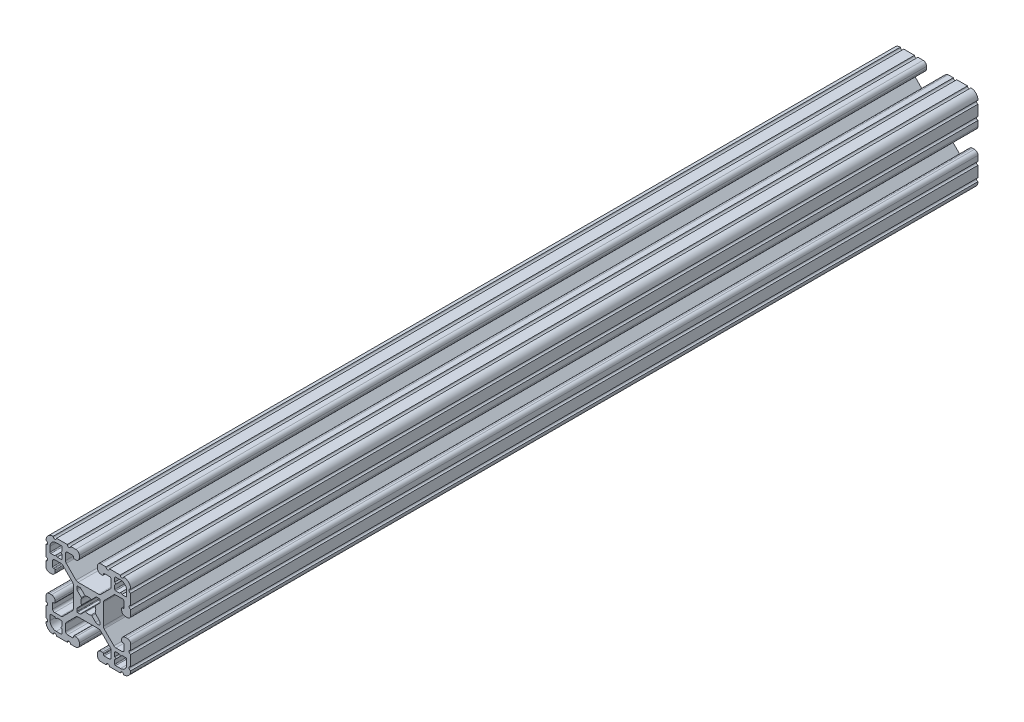
SolidWorks part; units mm, degrees
ref_plane "Front Plane" through (0, 0, 0) normal (0, 0, 1) x (1, 0, 0)
ref_plane "Top Plane" through (0, 0, 0) normal (0, 1, 0) x (1, 0, 0)
ref_plane "Right Plane" through (0, 0, 0) normal (1, 0, 0) x (0, 0, -1)
ref_plane "Plane1" through (0, 0, -2322.576) normal (0, 0, -1) x (-1, 0, 0)
sketch "Sketch1" plane through (0, 0, -2322.576) normal (0, 0, -1) x (-1, 0, 0)
  line L0 (17.2466, 14.4526) -> (17.2466, 12.2428)
  line L1 (16.8656, 11.8618) -> (15.0927, 11.8618)
  line L2 (15.0927, 11.8618) -> (14.5542, 12.4003)
  line L3 (14.5542, 12.4003) -> (14.0157, 11.8618)
  line L4 (14.0157, 11.8618) -> (12.2428, 11.8618)
  line L5 (11.8618, 12.2428) -> (11.8618, 14.0157)
  line L6 (11.8618, 14.0157) -> (12.4003, 14.5542)
  line L7 (12.4003, 14.5542) -> (11.8618, 15.0927)
  line L8 (11.8618, 15.0927) -> (11.8618, 16.8656)
  line L9 (12.2428, 17.2466) -> (14.4526, 17.2466)
  line L10 (17.2466, -12.2428) -> (17.2466, -14.4526)
  line L11 (14.4526, -17.2466) -> (12.2428, -17.2466)
  line L12 (11.8618, -16.8656) -> (11.8618, -15.0927)
  line L13 (11.8618, -15.0927) -> (12.4003, -14.5542)
  line L14 (12.4003, -14.5542) -> (11.8618, -14.0157)
  line L15 (11.8618, -14.0157) -> (11.8618, -12.2428)
  line L16 (12.2428, -11.8618) -> (14.0157, -11.8618)
  line L17 (14.0157, -11.8618) -> (14.5542, -12.4003)
  line L18 (14.5542, -12.4003) -> (15.0927, -11.8618)
  line L19 (15.0927, -11.8618) -> (16.8656, -11.8618)
  line L20 (5.1689, -3.9207) -> (5.1689, -4.9149)
  line L21 (4.9149, -5.1689) -> (3.9207, -5.1689)
  line L22 (3.2921, -4.9085) -> (1.5823, -3.1988)
  line L23 (-1.5823, -3.1988) -> (-3.2921, -4.9085)
  line L24 (-3.9207, -5.1689) -> (-4.9149, -5.1689)
  line L25 (-5.1689, -4.9149) -> (-5.1689, -3.9207)
  line L26 (-4.9085, -3.2921) -> (-3.1988, -1.5823)
  line L27 (-3.1988, 1.5823) -> (-4.9085, 3.2921)
  line L28 (-5.1689, 3.9207) -> (-5.1689, 4.9149)
  line L29 (-4.9149, 5.1689) -> (-3.9207, 5.1689)
  line L30 (-3.2921, 4.9085) -> (-1.5823, 3.1988)
  line L31 (1.5823, 3.1988) -> (3.2921, 4.9085)
  line L32 (3.9207, 5.1689) -> (4.9149, 5.1689)
  line L33 (5.1689, 4.9149) -> (5.1689, 3.9207)
  line L34 (4.9085, 3.2921) -> (3.1988, 1.5823)
  line L35 (3.1988, -1.5823) -> (4.9085, -3.2921)
  line L36 (-11.8618, -12.2428) -> (-11.8618, -14.0157)
  line L37 (-11.8618, -14.0157) -> (-12.4003, -14.5542)
  line L38 (-12.4003, -14.5542) -> (-11.8618, -15.0927)
  line L39 (-11.8618, -15.0927) -> (-11.8618, -16.8656)
  line L40 (-12.2428, -17.2466) -> (-14.4526, -17.2466)
  line L41 (-17.2466, -14.4526) -> (-17.2466, -12.2428)
  line L42 (-16.8656, -11.8618) -> (-15.0927, -11.8618)
  line L43 (-15.0927, -11.8618) -> (-14.5542, -12.4003)
  line L44 (-14.5542, -12.4003) -> (-14.0157, -11.8618)
  line L45 (-14.0157, -11.8618) -> (-12.2428, -11.8618)
  line L46 (-11.8618, 16.8656) -> (-11.8618, 15.0927)
  line L47 (-11.8618, 15.0927) -> (-12.4003, 14.5542)
  line L48 (-12.4003, 14.5542) -> (-11.8618, 14.0157)
  line L49 (-11.8618, 14.0157) -> (-11.8618, 12.2428)
  line L50 (-12.2428, 11.8618) -> (-14.0157, 11.8618)
  line L51 (-14.0157, 11.8618) -> (-14.5542, 12.4003)
  line L52 (-14.5542, 12.4003) -> (-15.0927, 11.8618)
  line L53 (-15.0927, 11.8618) -> (-16.8656, 11.8618)
  line L54 (-17.2466, 12.2428) -> (-17.2466, 14.4526)
  line L55 (-14.4526, 17.2466) -> (-12.2428, 17.2466)
  line L56 (19.05, -14.3256) -> (19.05, -9.4996)
  line L57 (19.05, -7.9756) -> (19.05, -5.6388)
  line L58 (17.4752, -4.064) -> (16.5608, -4.064)
  line L59 (14.986, -5.6388) -> (14.986, -6.35)
  line L60 (15.367, -6.731) -> (15.6972, -6.731)
  line L61 (16.0782, -7.112) -> (16.0782, -9.398)
  line L62 (15.1892, -10.287) -> (12.3756, -10.287)
  line L63 (11.4776, -9.915) -> (7.1157, -5.5531)
  line L64 (6.7437, -4.6551) -> (6.7437, 4.6551)
  line L65 (7.1157, 5.5531) -> (11.4776, 9.915)
  line L66 (12.3756, 10.287) -> (15.1892, 10.287)
  line L67 (16.0782, 9.398) -> (16.0782, 7.112)
  line L68 (15.6972, 6.731) -> (15.367, 6.731)
  line L69 (14.986, 6.35) -> (14.986, 5.6388)
  line L70 (16.5608, 4.064) -> (17.4752, 4.064)
  line L71 (19.05, 5.6388) -> (19.05, 7.9756)
  line L72 (19.05, 9.4996) -> (19.05, 14.3256)
  line L73 (14.3256, 19.05) -> (9.4996, 19.05)
  line L74 (7.9756, 19.05) -> (5.6388, 19.05)
  line L75 (4.064, 17.4752) -> (4.064, 16.5608)
  line L76 (5.6388, 14.986) -> (6.35, 14.986)
  line L77 (6.731, 15.367) -> (6.731, 15.6972)
  line L78 (7.112, 16.0782) -> (9.398, 16.0782)
  line L79 (10.287, 15.1892) -> (10.287, 12.3756)
  line L80 (9.915, 11.4776) -> (5.5531, 7.1157)
  line L81 (4.6551, 6.7437) -> (-4.6551, 6.7437)
  line L82 (-5.5531, 7.1157) -> (-9.915, 11.4776)
  line L83 (-10.287, 12.3756) -> (-10.287, 15.1892)
  line L84 (-9.398, 16.0782) -> (-7.112, 16.0782)
  line L85 (-6.731, 15.6972) -> (-6.731, 15.367)
  line L86 (-6.35, 14.986) -> (-5.6388, 14.986)
  line L87 (-4.064, 16.5608) -> (-4.064, 17.4752)
  line L88 (-5.6388, 19.05) -> (-7.9756, 19.05)
  line L89 (-9.4996, 19.05) -> (-14.3256, 19.05)
  line L90 (-19.05, 14.3256) -> (-19.05, 9.4996)
  line L91 (-19.05, 7.9756) -> (-19.05, 5.6388)
  line L92 (-17.4752, 4.064) -> (-16.5608, 4.064)
  line L93 (-14.986, 5.6388) -> (-14.986, 6.35)
  line L94 (-15.367, 6.731) -> (-15.6972, 6.731)
  line L95 (-16.0782, 7.112) -> (-16.0782, 9.398)
  line L96 (-15.1892, 10.287) -> (-12.3756, 10.287)
  line L97 (-11.4776, 9.915) -> (-7.1157, 5.5531)
  line L98 (-6.7437, 4.6551) -> (-6.7437, -4.6551)
  line L99 (-7.1157, -5.5531) -> (-11.4776, -9.915)
  line L100 (-12.3756, -10.287) -> (-15.1892, -10.287)
  line L101 (-16.0782, -9.398) -> (-16.0782, -7.112)
  line L102 (-15.6972, -6.731) -> (-15.367, -6.731)
  line L103 (-14.986, -6.35) -> (-14.986, -5.6388)
  line L104 (-16.5608, -4.064) -> (-17.4752, -4.064)
  line L105 (-19.05, -5.6388) -> (-19.05, -7.9756)
  line L106 (-19.05, -9.4996) -> (-19.05, -14.3256)
  line L107 (-14.3256, -19.05) -> (-9.4996, -19.05)
  line L108 (-7.9756, -19.05) -> (-5.6388, -19.05)
  line L109 (-4.064, -17.4752) -> (-4.064, -16.5608)
  line L110 (-5.6388, -14.986) -> (-6.35, -14.986)
  line L111 (-6.731, -15.367) -> (-6.731, -15.6972)
  line L112 (-7.112, -16.0782) -> (-9.398, -16.0782)
  line L113 (-10.287, -15.1892) -> (-10.287, -12.3756)
  line L114 (-9.915, -11.4776) -> (-5.5531, -7.1157)
  line L115 (-4.6551, -6.7437) -> (4.6551, -6.7437)
  line L116 (5.5531, -7.1157) -> (9.915, -11.4776)
  line L117 (10.287, -12.3756) -> (10.287, -15.1892)
  line L118 (9.398, -16.0782) -> (7.112, -16.0782)
  line L119 (6.731, -15.6972) -> (6.731, -15.367)
  line L120 (6.35, -14.986) -> (5.6388, -14.986)
  line L121 (4.064, -16.5608) -> (4.064, -17.4752)
  line L122 (5.6388, -19.05) -> (7.9756, -19.05)
  line L123 (9.4996, -19.05) -> (14.3256, -19.05)
  arc A0 (17.2466, 12.2428) -> (16.8656, 11.8618) centre (16.8656, 12.2428) cw
  arc A1 (12.2428, 11.8618) -> (11.8618, 12.2428) centre (12.2428, 12.2428) cw
  arc A2 (11.8618, 16.8656) -> (12.2428, 17.2466) centre (12.2428, 16.8656) cw
  arc A3 (14.4526, 17.2466) -> (17.2466, 14.4526) centre (14.4526, 14.4526) cw
  arc A4 (17.2466, -14.4526) -> (14.4526, -17.2466) centre (14.4526, -14.4526) cw
  arc A5 (12.2428, -17.2466) -> (11.8618, -16.8656) centre (12.2428, -16.8656) cw
  arc A6 (11.8618, -12.2428) -> (12.2428, -11.8618) centre (12.2428, -12.2428) cw
  arc A7 (16.8656, -11.8618) -> (17.2466, -12.2428) centre (16.8656, -12.2428) cw
  arc A8 (5.1689, -4.9149) -> (4.9149, -5.1689) centre (4.9149, -4.9149) cw
  arc A9 (3.9207, -5.1689) -> (3.2921, -4.9085) centre (3.9207, -4.2799) cw
  arc A10 (1.5823, -3.1988) -> (1.178, -3.1119) centre (1.3129, -3.4682) ccw
  arc A11 (1.178, -3.1119) -> (-1.178, -3.1119) centre (0, 0) cw
  arc A12 (-1.178, -3.1119) -> (-1.5823, -3.1988) centre (-1.3129, -3.4682) ccw
  arc A13 (-3.2921, -4.9085) -> (-3.9207, -5.1689) centre (-3.9207, -4.2799) cw
  arc A14 (-4.9149, -5.1689) -> (-5.1689, -4.9149) centre (-4.9149, -4.9149) cw
  arc A15 (-5.1689, -3.9207) -> (-4.9085, -3.2921) centre (-4.2799, -3.9207) cw
  arc A16 (-3.1988, -1.5823) -> (-3.1119, -1.178) centre (-3.4682, -1.3129) ccw
  arc A17 (-3.1119, -1.178) -> (-3.1119, 1.178) centre (0, 0) cw
  arc A18 (-3.1119, 1.178) -> (-3.1988, 1.5823) centre (-3.4682, 1.3129) ccw
  arc A19 (-4.9085, 3.2921) -> (-5.1689, 3.9207) centre (-4.2799, 3.9207) cw
  arc A20 (-5.1689, 4.9149) -> (-4.9149, 5.1689) centre (-4.9149, 4.9149) cw
  arc A21 (-3.9207, 5.1689) -> (-3.2921, 4.9085) centre (-3.9207, 4.2799) cw
  arc A22 (-1.5823, 3.1988) -> (-1.178, 3.1119) centre (-1.3129, 3.4682) ccw
  arc A23 (-1.178, 3.1119) -> (1.178, 3.1119) centre (0, 0) cw
  arc A24 (1.178, 3.1119) -> (1.5823, 3.1988) centre (1.3129, 3.4682) ccw
  arc A25 (3.2921, 4.9085) -> (3.9207, 5.1689) centre (3.9207, 4.2799) cw
  arc A26 (4.9149, 5.1689) -> (5.1689, 4.9149) centre (4.9149, 4.9149) cw
  arc A27 (5.1689, 3.9207) -> (4.9085, 3.2921) centre (4.2799, 3.9207) cw
  arc A28 (3.1988, 1.5823) -> (3.1119, 1.178) centre (3.4682, 1.3129) ccw
  arc A29 (3.1119, 1.178) -> (3.1119, -1.178) centre (0, 0) cw
  arc A30 (3.1119, -1.178) -> (3.1988, -1.5823) centre (3.4682, -1.3129) ccw
  arc A31 (4.9085, -3.2921) -> (5.1689, -3.9207) centre (4.2799, -3.9207) cw
  arc A32 (-11.8618, -16.8656) -> (-12.2428, -17.2466) centre (-12.2428, -16.8656) cw
  arc A33 (-14.4526, -17.2466) -> (-17.2466, -14.4526) centre (-14.4526, -14.4526) cw
  arc A34 (-17.2466, -12.2428) -> (-16.8656, -11.8618) centre (-16.8656, -12.2428) cw
  arc A35 (-12.2428, -11.8618) -> (-11.8618, -12.2428) centre (-12.2428, -12.2428) cw
  arc A36 (-12.2428, 17.2466) -> (-11.8618, 16.8656) centre (-12.2428, 16.8656) cw
  arc A37 (-11.8618, 12.2428) -> (-12.2428, 11.8618) centre (-12.2428, 12.2428) cw
  arc A38 (-16.8656, 11.8618) -> (-17.2466, 12.2428) centre (-16.8656, 12.2428) cw
  arc A39 (-17.2466, 14.4526) -> (-14.4526, 17.2466) centre (-14.4526, 14.4526) cw
  arc A40 (19.05, -9.4996) -> (19.05, -7.9756) centre (19.05, -8.7376) cw
  arc A41 (19.05, -5.6388) -> (17.4752, -4.064) centre (17.4752, -5.6388) ccw
  arc A42 (16.5608, -4.064) -> (14.986, -5.6388) centre (16.5608, -5.6388) ccw
  arc A43 (14.986, -6.35) -> (15.367, -6.731) centre (15.367, -6.35) ccw
  arc A44 (15.6972, -6.731) -> (16.0782, -7.112) centre (15.6972, -7.112) cw
  arc A45 (16.0782, -9.398) -> (15.1892, -10.287) centre (15.1892, -9.398) cw
  arc A46 (12.3756, -10.287) -> (11.4776, -9.915) centre (12.3756, -9.017) cw
  arc A47 (7.1157, -5.5531) -> (6.7437, -4.6551) centre (8.0137, -4.6551) cw
  arc A48 (6.7437, 4.6551) -> (7.1157, 5.5531) centre (8.0137, 4.6551) cw
  arc A49 (11.4776, 9.915) -> (12.3756, 10.287) centre (12.3756, 9.017) cw
  arc A50 (15.1892, 10.287) -> (16.0782, 9.398) centre (15.1892, 9.398) cw
  arc A51 (16.0782, 7.112) -> (15.6972, 6.731) centre (15.6972, 7.112) cw
  arc A52 (15.367, 6.731) -> (14.986, 6.35) centre (15.367, 6.35) ccw
  arc A53 (14.986, 5.6388) -> (16.5608, 4.064) centre (16.5608, 5.6388) ccw
  arc A54 (17.4752, 4.064) -> (19.05, 5.6388) centre (17.4752, 5.6388) ccw
  arc A55 (19.05, 7.9756) -> (19.05, 9.4996) centre (19.05, 8.7376) cw
  arc A56 (19.05, 14.3256) -> (19.0499, 15.8496) centre (19.05, 15.0876) cw
  arc A57 (19.0499, 15.8496) -> (15.8496, 19.0499) centre (15.875, 15.875) ccw
  arc A58 (15.8496, 19.0499) -> (14.3256, 19.05) centre (15.0876, 19.05) cw
  arc A59 (9.4996, 19.05) -> (7.9756, 19.05) centre (8.7376, 19.05) cw
  arc A60 (5.6388, 19.05) -> (4.064, 17.4752) centre (5.6388, 17.4752) ccw
  arc A61 (4.064, 16.5608) -> (5.6388, 14.986) centre (5.6388, 16.5608) ccw
  arc A62 (6.35, 14.986) -> (6.731, 15.367) centre (6.35, 15.367) ccw
  arc A63 (6.731, 15.6972) -> (7.112, 16.0782) centre (7.112, 15.6972) cw
  arc A64 (9.398, 16.0782) -> (10.287, 15.1892) centre (9.398, 15.1892) cw
  arc A65 (10.287, 12.3756) -> (9.915, 11.4776) centre (9.017, 12.3756) cw
  arc A66 (5.5531, 7.1157) -> (4.6551, 6.7437) centre (4.6551, 8.0137) cw
  arc A67 (-4.6551, 6.7437) -> (-5.5531, 7.1157) centre (-4.6551, 8.0137) cw
  arc A68 (-9.915, 11.4776) -> (-10.287, 12.3756) centre (-9.017, 12.3756) cw
  arc A69 (-10.287, 15.1892) -> (-9.398, 16.0782) centre (-9.398, 15.1892) cw
  arc A70 (-7.112, 16.0782) -> (-6.731, 15.6972) centre (-7.112, 15.6972) cw
  arc A71 (-6.731, 15.367) -> (-6.35, 14.986) centre (-6.35, 15.367) ccw
  arc A72 (-5.6388, 14.986) -> (-4.064, 16.5608) centre (-5.6388, 16.5608) ccw
  arc A73 (-4.064, 17.4752) -> (-5.6388, 19.05) centre (-5.6388, 17.4752) ccw
  arc A74 (-7.9756, 19.05) -> (-9.4996, 19.05) centre (-8.7376, 19.05) cw
  arc A75 (-14.3256, 19.05) -> (-15.8496, 19.0499) centre (-15.0876, 19.05) cw
  arc A76 (-15.8496, 19.0499) -> (-19.0499, 15.8496) centre (-15.875, 15.875) ccw
  arc A77 (-19.0499, 15.8496) -> (-19.05, 14.3256) centre (-19.05, 15.0876) cw
  arc A78 (-19.05, 9.4996) -> (-19.05, 7.9756) centre (-19.05, 8.7376) cw
  arc A79 (-19.05, 5.6388) -> (-17.4752, 4.064) centre (-17.4752, 5.6388) ccw
  arc A80 (-16.5608, 4.064) -> (-14.986, 5.6388) centre (-16.5608, 5.6388) ccw
  arc A81 (-14.986, 6.35) -> (-15.367, 6.731) centre (-15.367, 6.35) ccw
  arc A82 (-15.6972, 6.731) -> (-16.0782, 7.112) centre (-15.6972, 7.112) cw
  arc A83 (-16.0782, 9.398) -> (-15.1892, 10.287) centre (-15.1892, 9.398) cw
  arc A84 (-12.3756, 10.287) -> (-11.4776, 9.915) centre (-12.3756, 9.017) cw
  arc A85 (-7.1157, 5.5531) -> (-6.7437, 4.6551) centre (-8.0137, 4.6551) cw
  arc A86 (-6.7437, -4.6551) -> (-7.1157, -5.5531) centre (-8.0137, -4.6551) cw
  arc A87 (-11.4776, -9.915) -> (-12.3756, -10.287) centre (-12.3756, -9.017) cw
  arc A88 (-15.1892, -10.287) -> (-16.0782, -9.398) centre (-15.1892, -9.398) cw
  arc A89 (-16.0782, -7.112) -> (-15.6972, -6.731) centre (-15.6972, -7.112) cw
  arc A90 (-15.367, -6.731) -> (-14.986, -6.35) centre (-15.367, -6.35) ccw
  arc A91 (-14.986, -5.6388) -> (-16.5608, -4.064) centre (-16.5608, -5.6388) ccw
  arc A92 (-17.4752, -4.064) -> (-19.05, -5.6388) centre (-17.4752, -5.6388) ccw
  arc A93 (-19.05, -7.9756) -> (-19.05, -9.4996) centre (-19.05, -8.7376) cw
  arc A94 (-19.05, -14.3256) -> (-19.0499, -15.8496) centre (-19.05, -15.0876) cw
  arc A95 (-19.0499, -15.8496) -> (-15.8496, -19.0499) centre (-15.875, -15.875) ccw
  arc A96 (-15.8496, -19.0499) -> (-14.3256, -19.05) centre (-15.0876, -19.05) cw
  arc A97 (-9.4996, -19.05) -> (-7.9756, -19.05) centre (-8.7376, -19.05) cw
  arc A98 (-5.6388, -19.05) -> (-4.064, -17.4752) centre (-5.6388, -17.4752) ccw
  arc A99 (-4.064, -16.5608) -> (-5.6388, -14.986) centre (-5.6388, -16.5608) ccw
  arc A100 (-6.35, -14.986) -> (-6.731, -15.367) centre (-6.35, -15.367) ccw
  arc A101 (-6.731, -15.6972) -> (-7.112, -16.0782) centre (-7.112, -15.6972) cw
  arc A102 (-9.398, -16.0782) -> (-10.287, -15.1892) centre (-9.398, -15.1892) cw
  arc A103 (-10.287, -12.3756) -> (-9.915, -11.4776) centre (-9.017, -12.3756) cw
  arc A104 (-5.5531, -7.1157) -> (-4.6551, -6.7437) centre (-4.6551, -8.0137) cw
  arc A105 (4.6551, -6.7437) -> (5.5531, -7.1157) centre (4.6551, -8.0137) cw
  arc A106 (9.915, -11.4776) -> (10.287, -12.3756) centre (9.017, -12.3756) cw
  arc A107 (10.287, -15.1892) -> (9.398, -16.0782) centre (9.398, -15.1892) cw
  arc A108 (7.112, -16.0782) -> (6.731, -15.6972) centre (7.112, -15.6972) cw
  arc A109 (6.731, -15.367) -> (6.35, -14.986) centre (6.35, -15.367) ccw
  arc A110 (5.6388, -14.986) -> (4.064, -16.5608) centre (5.6388, -16.5608) ccw
  arc A111 (4.064, -17.4752) -> (5.6388, -19.05) centre (5.6388, -17.4752) ccw
  arc A112 (7.9756, -19.05) -> (9.4996, -19.05) centre (8.7376, -19.05) cw
  arc A113 (14.3256, -19.05) -> (15.8496, -19.0499) centre (15.0876, -19.05) cw
  arc A114 (15.8496, -19.0499) -> (19.0499, -15.8496) centre (15.875, -15.875) ccw
  arc A115 (19.0499, -15.8496) -> (19.05, -14.3256) centre (19.05, -15.0876) cw
extrude "Boss-Extrude1" add sketch "Sketch1" against normal blind 381
